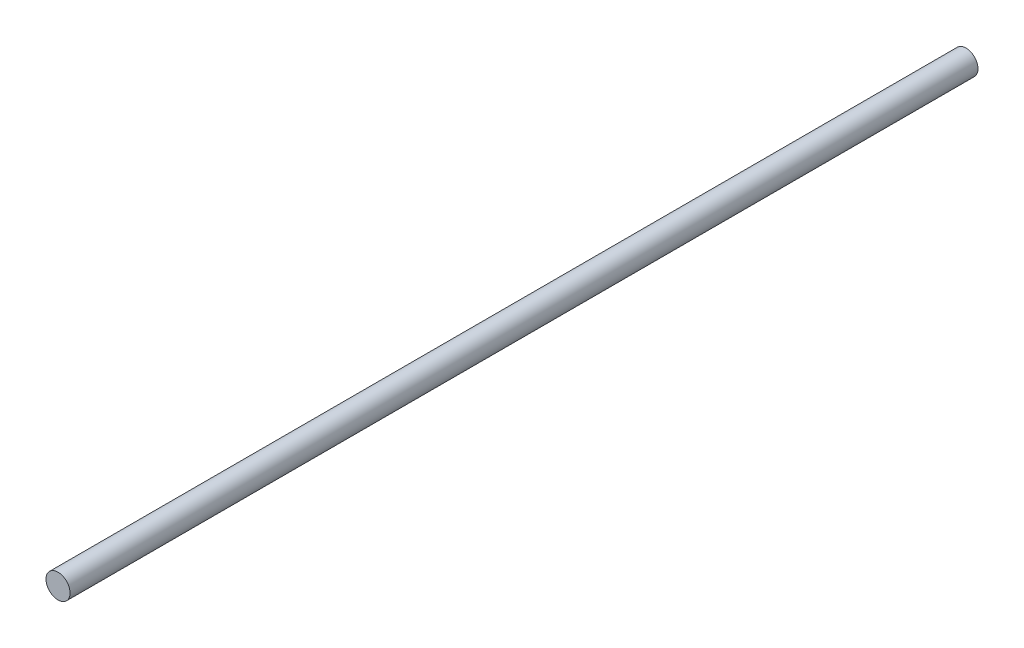
SolidWorks part; units mm, degrees
ref_plane "Front" through (0, 0, 0) normal (0, 0, 1) x (1, 0, 0)
ref_plane "Top" through (0, 0, 0) normal (0, 1, 0) x (1, 0, 0)
ref_plane "Right" through (0, 0, 0) normal (1, 0, 0) x (0, 0, -1)
sketch "草图1" plane through (0, 0, 0) normal (0, 0, 1) x (1, 0, 0)
  circle A0 centre (0, 0) radius 0.325
  dimension "D1" = 0.65
extrude "凸台-拉伸1" add sketch "草图1" along normal blind 24.5
